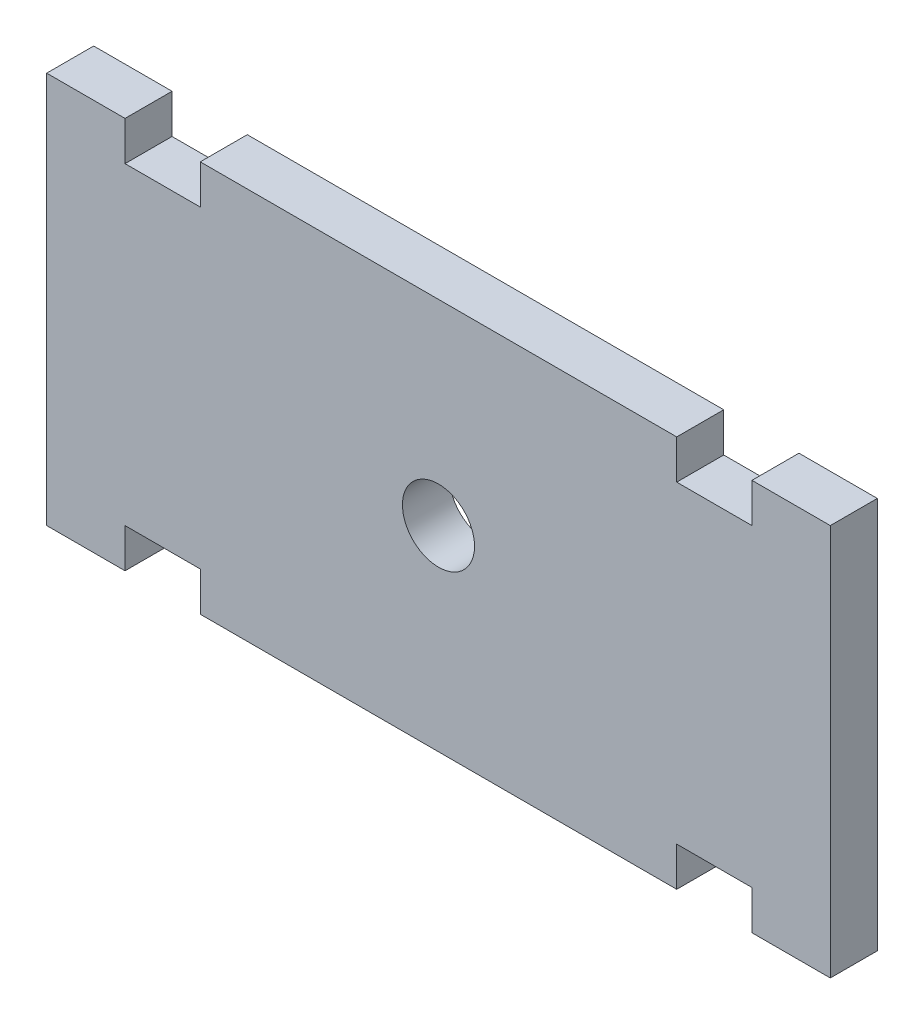
SolidWorks part; units mm, degrees
ref_plane "Front Plane" through (0, 0, 0) normal (0, 0, 1) x (1, 0, 0)
ref_plane "Top Plane" through (0, 0, 0) normal (0, 1, 0) x (1, 0, 0)
ref_plane "Right Plane" through (0, 0, 0) normal (1, 0, 0) x (0, 0, -1)
sketch "Sketch1" plane through (0, 0, 0) normal (0, 0, 1) x (1, 0, 0)
  line L0 (-20, 12.5) -> (-20, 10)
  line L1 (-25, 12.5) -> (-20, 12.5)
  line L2 (-25, 12.5) -> (-25, -12.5)
  line L3 (-25, -12.5) -> (-20, -12.5)
  line L4 (15.2, -10) -> (15.2, -12.5)
  line L5 (-20, 10) -> (-15.2, 10)
  line L6 (-15.2, 10) -> (-15.2, 12.5)
  line L10 (-15.2, 12.5) -> (15.2, 12.5)
  line L11 (-20, -12.5) -> (-20, -10)
  line L12 (-20, -10) -> (-15.2, -10)
  line L13 (-15.2, -10) -> (-15.2, -12.5)
  line L14 (-15.2, -12.5) -> (15.2, -12.5)
  line L20 (20, -10) -> (15.2, -10)
  line L21 (20, -12.5) -> (20, -10)
  line L22 (15.2, 10) -> (15.2, 12.5)
  line L23 (20, 10) -> (15.2, 10)
  line L24 (25, -12.5) -> (20, -12.5)
  line L25 (25, 12.5) -> (25, -12.5)
  line L26 (25, 12.5) -> (20, 12.5)
  line L27 (20, 12.5) -> (20, 10)
  line L28 (0, 12.5) -> (0, -12.5) construction
  point P28 (0, 12.5)
  dimension "D1" = 4.8
  dimension "D2" = 5
  dimension "D3" = 25
  dimension "D4" = 10
  dimension "D5" = 12.5
  dimension "D6" = 10
extrude "Boss-Extrude1" add sketch "Sketch1" against normal blind 3
sketch "Sketch2" plane through (0, 0, 0) normal (0, 0, 1) x (1, 0, 0)
  line L0 (15.2, 12.5) -> (-15.2, 12.5) construction
  line L1 (25, -12.5) -> (25, 12.5) construction
  circle A0 centre (0, 0) radius 2.3
  dimension "D1" = 4.6
  dimension "D2" = 12.5
  dimension "D3" = 25
extrude "Cut-Extrude1" cut sketch "Sketch2" against normal blind 3
